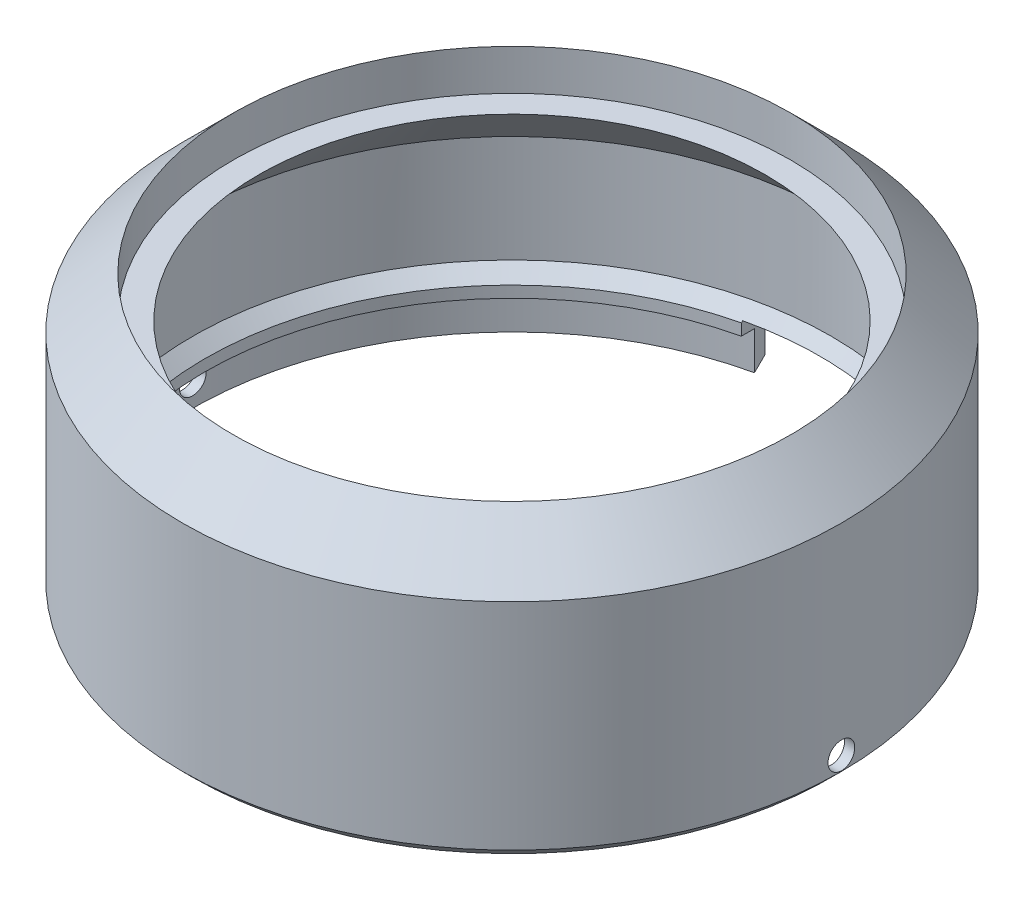
SolidWorks part; units mm, degrees
ref_plane "Front Plane" through (0, 0, 0) normal (0, 0, 1) x (1, 0, 0)
ref_plane "Top Plane" through (0, 0, 0) normal (0, 1, 0) x (1, 0, 0)
ref_plane "Right Plane" through (0, 0, 0) normal (1, 0, 0) x (0, 0, -1)
sketch "Sketch1" plane through (0, 0, 0) normal (0, 0, 1) x (1, 0, 0)
  line L0 (0, 0) -> (25, 0) construction
  line L1 (25, 0) -> (25, -4) construction
  line L2 (25, -4) -> (24, -5) construction
  line L3 (24, -5) -> (0, -5) construction
  line L4 (0, -5) -> (0, 0) construction
  line L5 (24, 0) -> (24, -1) construction
  line L6 (24, -1) -> (25, -1) construction
  line L7 (25, -2) -> (0, -2) construction
  line L8 (25.1, 1) -> (24.1, 0)
  line L9 (24.1, 0) -> (24.1, -0.9)
  line L10 (24.1, -0.9) -> (25.1, -0.9)
  line L11 (25.1, -0.9) -> (25.1, -3.9)
  line L12 (25.1, -3.9) -> (25.9, -3.1)
  line L13 (25.9, -3.1) -> (25.9, 13.8)
  line L14 (25.9, 13.8) -> (21.9, 17.8)
  line L15 (21.9, 17.8) -> (21.9, 14.6)
  line L16 (21.9, 14.6) -> (19.9, 14.6)
  line L17 (19.9, 14.6) -> (25.1, 9.4)
  line L18 (25.1, 9.4) -> (25.1, 1)
  line L19 (0, -4.2) -> (15, -4.2) construction
  line L20 (15, -4.2) -> (15, -5) construction
  dimension "D1" = 135
  dimension "D2" = 1
  dimension "D3" = 25
  dimension "D4" = 5
  dimension "D5" = 1
  dimension "D6" = 1
  dimension "D7" = 2
  dimension "D8" = 3.2
  dimension "D9" = 2
  dimension "D10" = 0.1
  dimension "D11" = 0.1
  dimension "D12" = 0.1
  dimension "D13" = 0.8
  dimension "D14" = 4
  dimension "D15" = 0.8
  dimension "D16" = 15
  dimension "D17" = 18.8
revolve "Revolve1" add sketch "Sketch1" angle 360 about L4
sketch "Sketch2" plane through (0, 0, 0) normal (0, 0, 1) x (1, 0, 0)
  line L0 (0, 0) -> (0, 0.1) construction
  line L1 (-5.45, -4.2) -> (5.45, -4.2)
  line L2 (-5.45, -4.2) -> (-5.45, 0.1)
  line L3 (-5.45, 0.1) -> (5.45, 0.1)
  line L4 (5.45, -4.2) -> (5.45, 0.1)
  line L5 (24.1, 0) -> (-24.1, 0) construction
  dimension "D1" = 10.9
  dimension "D2" = 4.3
  dimension "D3" = 4.2
extrude "Cut-Extrude1" cut sketch "Sketch2" against normal through all
sketch "Sketch3" plane through (0, 0, 0) normal (1, 0, 0) x (0, 0, -1)
  line L0 (23.4757, 0) -> (-24.1, 0) construction
  line L1 (0, -2) -> (0, 0) construction
  circle A0 centre (0, -2) radius 1.05
  dimension "D1" = 2.1
  dimension "D2" = 2
extrude "Cut-Extrude2" cut sketch "Sketch3" against normal through all both and the other way through all
